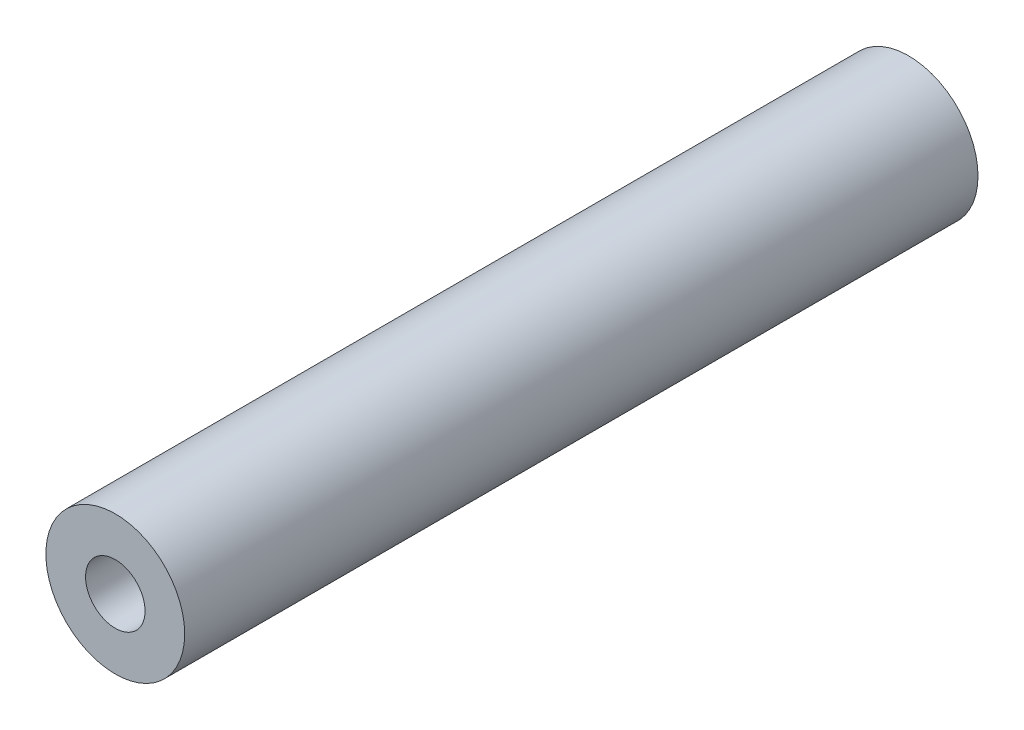
SolidWorks part; units mm, degrees
ref_plane "Alzado" through (0, 0, 0) normal (0, 0, 1) x (1, 0, 0)
ref_plane "Planta" through (0, 0, 0) normal (0, 1, 0) x (1, 0, 0)
ref_plane "Vista lateral" through (0, 0, 0) normal (1, 0, 0) x (0, 0, -1)
sketch "Croquis1" plane through (0, 0, 0) normal (0, 0, 1) x (1, 0, 0)
  circle A0 centre (0, 0) radius 3.5
  dimension "D1" = 7
extrude "Saliente-Extruir1" add sketch "Croquis1" along normal blind 40
sketch "Croquis2" plane through (0, 0, 40) normal (0, 0, 1) x (1, 0, 0)
  circle A0 centre (0, 0) radius 1.5
  dimension "D1" = 3
extrude "Cortar-Extruir1" cut sketch "Croquis2" against normal blind 15
sketch "Croquis3" plane through (0, 0, 0) normal (0, 0, -1) x (-1, 0, 0)
  circle A0 centre (0, 0) radius 2
  dimension "D1" = 4
extrude "Cortar-Extruir2" cut sketch "Croquis3" against normal blind 15
sketch "Croquis4" plane through (0, 0, 0) normal (0, 1, 0) x (1, 0, 0)
  line L0 (-3.5, -40) -> (3.5, -40) construction
  line L1 (3.5, 0) -> (-3.5, 0) construction
  circle A0 centre (0, -4) radius 1.4
  circle A1 centre (0, -36) radius 1.4
  dimension "D1" = 2.8
  dimension "D2" = 2.8
  dimension "D3" = 4
  dimension "D4" = 4
extrude "Cortar-Extruir3" cut sketch "Croquis4" against normal through all
